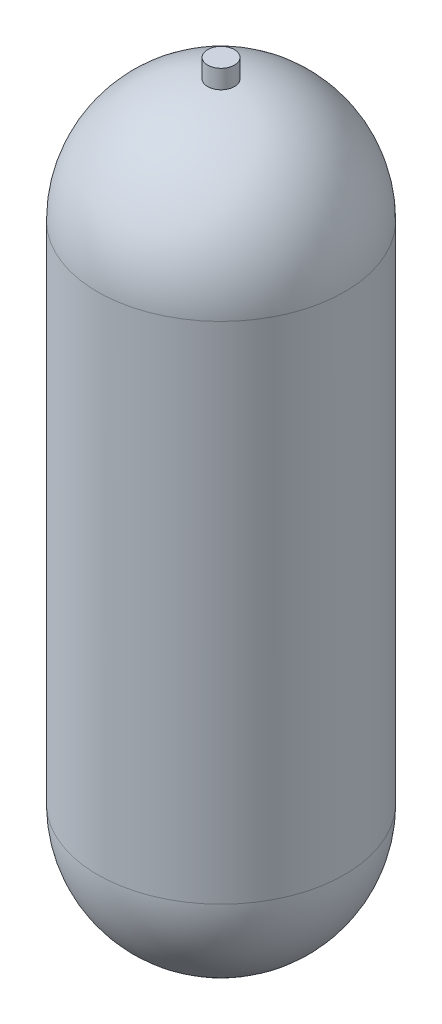
SolidWorks part; units mm, degrees
material "A-Glass Fiber"
ref_plane "Front Plane" through (0, 0, 0) normal (0, 0, 1) x (1, 0, 0)
ref_plane "Top Plane" through (0, 0, 0) normal (0, 1, 0) x (1, 0, 0)
ref_plane "Right Plane" through (0, 0, 0) normal (1, 0, 0) x (0, 0, -1)
sketch "Sketch1" plane through (0, 0, 0) normal (0, 0, 1) x (1, 0, 0)
  line L0 (-277.9989, 0) -> (285.3595, 0) construction
  line L1 (87.63, 445.77) -> (87.63, 87.63)
  line L2 (-223.1734, 533.4) -> (246.1876, 533.4) construction
  line L3 (0, -16.2482) -> (0, 0) construction
  line L4 (84.455, 445.77) -> (84.455, 87.63)
  line L5 (0, 533.4) -> (0, 540.8646) construction
  line L6 (0, 530.225) -> (0, 533.4)
  line L7 (0, 3.175) -> (0, 0)
  arc A0 (0, 0) -> (87.63, 87.63) centre (0, 87.63) ccw
  arc A1 (87.63, 445.77) -> (0, 533.4) centre (0, 445.77) ccw
  arc A2 (84.455, 445.77) -> (0, 530.225) centre (0, 445.77) ccw
  arc A3 (0, 3.175) -> (84.455, 87.63) centre (0, 87.63) ccw
  dimension "D1" = 533.4
  dimension "D2" = 87.63
  dimension "D3" = 3.175
revolve "Revolve1" add sketch "Sketch1" angle 360 about L5
ref_plane "Plane1" through (0, 533.4, 0) normal (0, 1, 0) x (1, 0, 0)
sketch "Sketch2" plane through (0, 533.4, 0) normal (0, 1, 0) x (1, 0, 0)
  circle A0 centre (0, 0) radius 9.525
  dimension "D1" = 19.05
extrude "Boss-Extrude1" add sketch "Sketch2" along normal blind 12.7 and the other way up to next contours A0
sketch "Sketch3" plane through (0, 546.1, 0) normal (0, 1, 0) x (1, 0, 0)
  line L0 (0, 28.2988) -> (0, -59.228) construction
  line L1 (-76.1012, 0) -> (75.6366, 0) construction
